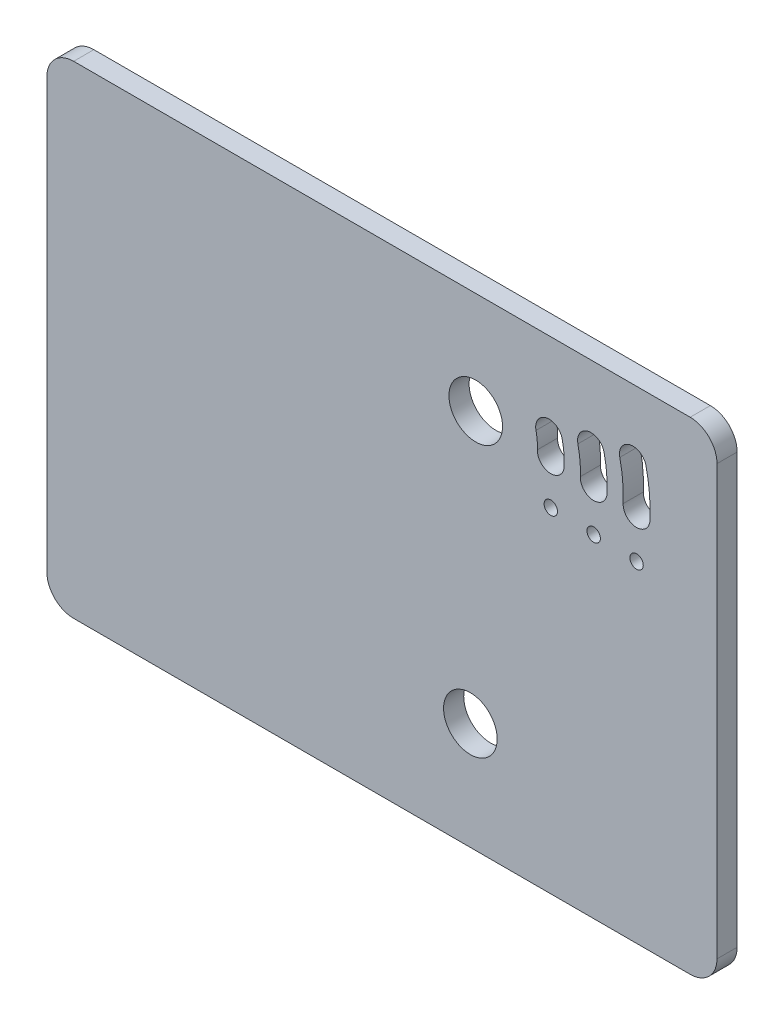
SolidWorks part; units mm, degrees
material "1060 Alloy"
ref_plane "Front Plane" through (0, 0, 0) normal (0, 0, 1) x (1, 0, 0)
ref_plane "Top Plane" through (0, 0, 0) normal (0, 1, 0) x (1, 0, 0)
ref_plane "Right Plane" through (0, 0, 0) normal (1, 0, 0) x (0, 0, -1)
sketch "Sketch1" plane through (0, 0, 0) normal (0, 0, 1) x (1, 0, 0)
  line L0 (101.6, 90.17) -> (101.6, 114.3) construction
  line L1 (0, 0) -> (158.75, 0)
  line L2 (0, 0) -> (0, 114.3)
  line L3 (0, 114.3) -> (158.75, 114.3)
  line L4 (158.75, 0) -> (158.75, 114.3)
  line L10 (119.38, 0) -> (119.38, 79.2337) construction
  line L11 (129.54, 0) -> (129.54, 78.7901) construction
  line L12 (139.7, 0) -> (139.7, 78.3465) construction
  line L13 (101.6, 90.17) -> (119.38, 89.3937) construction
  line L14 (119.38, 89.3937) -> (139.7, 88.5065) construction
  line L15 (139.7, 88.5065) -> (129.54, 88.9501) construction
  line L16 (101.6, 90.17) -> (118.9751, 94.022) construction
  line L17 (118.9751, 94.022) -> (118.0591, 93.8189) construction
  line L18 (118.0591, 93.8189) -> (138.8323, 98.4242) construction
  line L19 (138.8323, 98.4242) -> (128.9037, 96.2231) construction
  line L20 (119.38, 89.3937) -> (119.38, 79.2337) construction
  line L21 (129.54, 88.9501) -> (129.54, 78.7901) construction
  line L22 (139.7, 88.5065) -> (139.7, 78.3465) construction
  circle A0 centre (101.6, 90.17) radius 6.35
  circle A1 centre (119.38, 79.2337) radius 1.5875
  circle A2 centre (129.54, 78.7901) radius 1.5875
  circle A3 centre (139.7, 78.3465) radius 1.5875
  arc A4 (119.38, 89.3937) -> (118.9751, 94.022) centre (101.6, 90.17) ccw construction
  arc A5 (122.552, 89.2552) -> (122.0748, 94.7092) centre (101.6, 90.17) ccw
  arc A6 (116.208, 89.5322) -> (115.8753, 93.3348) centre (101.6, 90.17) ccw
  arc A7 (116.208, 89.5322) -> (122.552, 89.2552) centre (119.38, 89.3937) ccw
  arc A8 (122.0748, 94.7092) -> (115.8753, 93.3348) centre (118.9751, 94.022) ccw
  arc A9 (139.7, 88.5065) -> (138.8323, 98.4242) centre (101.6, 90.17) ccw construction
  arc A10 (142.872, 88.368) -> (141.9321, 99.1114) centre (101.6, 90.17) ccw
  arc A11 (136.528, 88.645) -> (135.7326, 97.737) centre (101.6, 90.17) ccw
  arc A12 (136.528, 88.645) -> (142.872, 88.368) centre (139.7, 88.5065) ccw
  arc A13 (141.9321, 99.1114) -> (135.7326, 97.737) centre (138.8323, 98.4242) ccw
  arc A14 (129.54, 88.9501) -> (128.9037, 96.2231) centre (101.6, 90.17) ccw construction
  arc A15 (132.712, 88.8116) -> (132.0034, 96.9103) centre (101.6, 90.17) ccw
  arc A16 (126.368, 89.0886) -> (125.804, 95.5359) centre (101.6, 90.17) ccw
  arc A17 (126.368, 89.0886) -> (132.712, 88.8116) centre (129.54, 88.9501) ccw
  arc A18 (132.0034, 96.9103) -> (125.804, 95.5359) centre (128.9037, 96.2231) ccw
  point P23 (119.3292, 91.7211)
  point P30 (139.5912, 93.4938)
  point P38 (129.4602, 92.6075)
  dimension "D6" = 12.7
  dimension "D10" = 3.175
  dimension "D12" = 3.175
  dimension "D1" = 114.3
  dimension "D2" = 158.75
  dimension "D3" = 92.5
  dimension "D4" = 10.16
  dimension "D5" = 101.6
  dimension "D7" = 10.16
  dimension "D8" = 24.13
  dimension "D9" = 10.16
  dimension "D11" = 10.16
  dimension "D13" = 15
  dimension "D14" = 10.16
  dimension "D15" = 17.78
extrude "Boss-Extrude1" add sketch "Sketch1" along normal blind 4.7752
fillet "Fillet2" radius 6.35 4 edges at (158.75, 0, 2.3876) (0, 0, 2.3876) (158.75, 114.3, 2.3876) (0, 114.3, 2.3876)
sketch "Sketch2" plane through (0, 0, 4.7752) normal (0, 0, 1) x (1, 0, 0)
  line L0 (152.4, 114.3) -> (6.35, 114.3) construction
  line L4 (100.33, 25.4) -> (158.75, 25.4) construction
  line L5 (158.75, 6.35) -> (158.75, 107.95) construction
  circle A0 centre (100.33, 25.4) radius 6.35
  dimension "D1" = 12.7
  dimension "D2" = 88.9
  dimension "D3" = 58.42
extrude "Cut-Extrude1" cut sketch "Sketch2" against normal blind 20.32
